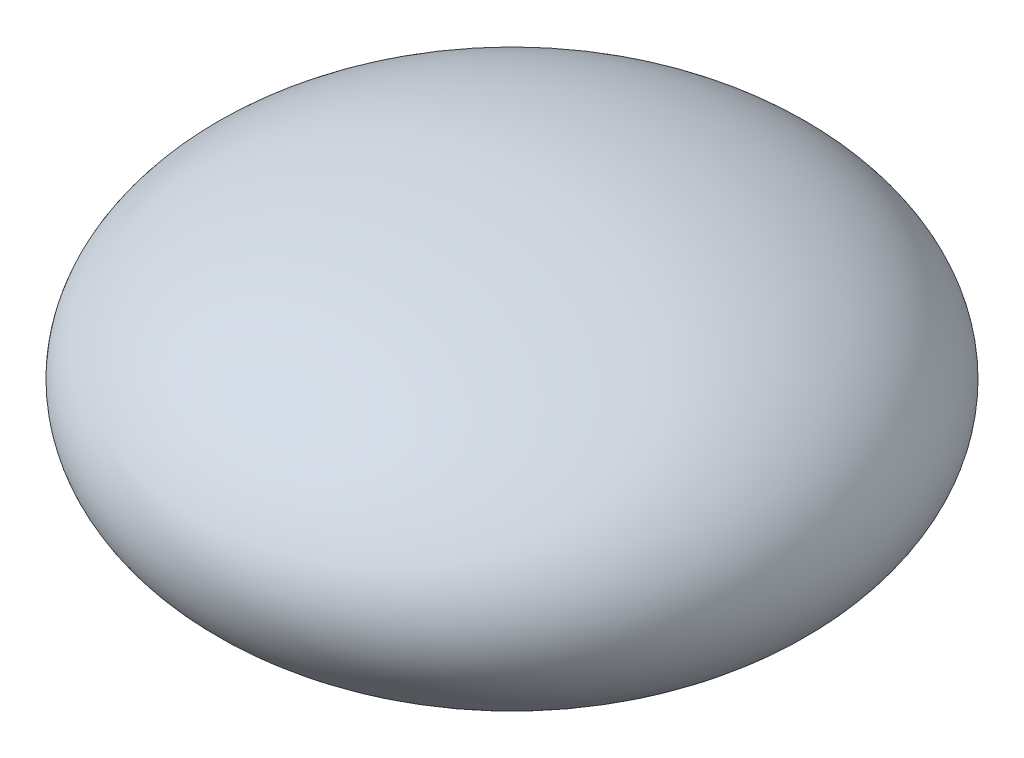
SolidWorks part; units mm, degrees
ref_plane "Front Plane" through (0, 0, 0) normal (0, 0, 1) x (1, 0, 0)
ref_plane "Top Plane" through (0, 0, 0) normal (0, 1, 0) x (1, 0, 0)
ref_plane "Right Plane" through (0, 0, 0) normal (1, 0, 0) x (0, 0, -1)
sketch "Sketch3" plane through (0, 0, 0) normal (0, 0, 1) x (1, 0, 0)
  line L0 (0, 5.5) -> (0, -5.5)
  line L1 (-10.75, -5.5) -> (10.75, -5.5) construction
  line L2 (-10.75, -5.5) -> (-10.75, 5.5) construction
  line L3 (-10.75, 5.5) -> (10.75, 5.5) construction
  line L4 (10.75, -5.5) -> (10.75, 5.5) construction
  line L5 (-10.75, -5.5) -> (10.75, 5.5) construction
  line L6 (-10.75, 5.5) -> (10.75, -5.5) construction
  ellipse E0 centre (0, 0) end of major axis (10.75, 0) minor radius 5.5 (0, 5.5) -> (0, -5.5) cw
  point P1 (0, 0)
  point P7 (0, 0)
  dimension "D1" = 11
  dimension "D2" = 21.5
revolve "Revolve3" add sketch "Sketch3" angle 360 about L0
